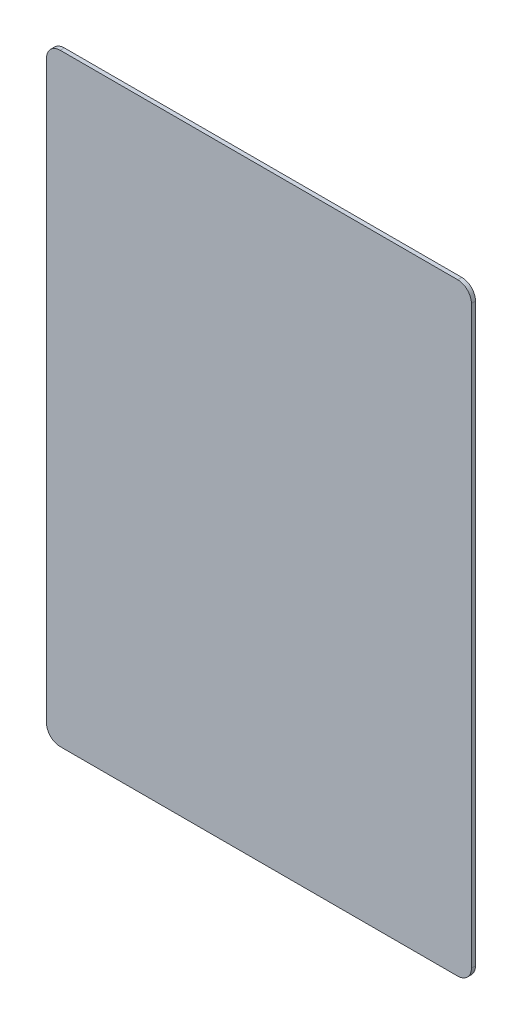
SolidWorks part; units mm, degrees
material "Balsa"
ref_plane "前视基准面" through (0, 0, 0) normal (0, 0, 1) x (1, 0, 0)
ref_plane "上视基准面" through (0, 0, 0) normal (0, 1, 0) x (1, 0, 0)
ref_plane "右视基准面" through (0, 0, 0) normal (1, 0, 0) x (0, 0, -1)
other "Configuration Table"
sketch "Sketch1" plane through (0, 0, 0) normal (0, 0, 1) x (1, 0, 0)
  line L1 (0, 0) -> (310, 0)
  line L2 (0, 0) -> (0, 440)
  line L3 (0, 440) -> (310, 440)
  line L4 (310, 0) -> (310, 440)
  dimension "D1" = 310
  dimension "D2" = 440
extrude "Boss-Extrude1" add sketch "Sketch1" along normal blind 3 contours L2 L1 L4 L3
fillet "Fillet1" radius 10 4 edges at (310, 0, 1.5) (0, 0, 1.5) (310, 440, 1.5) (0, 440, 1.5)
